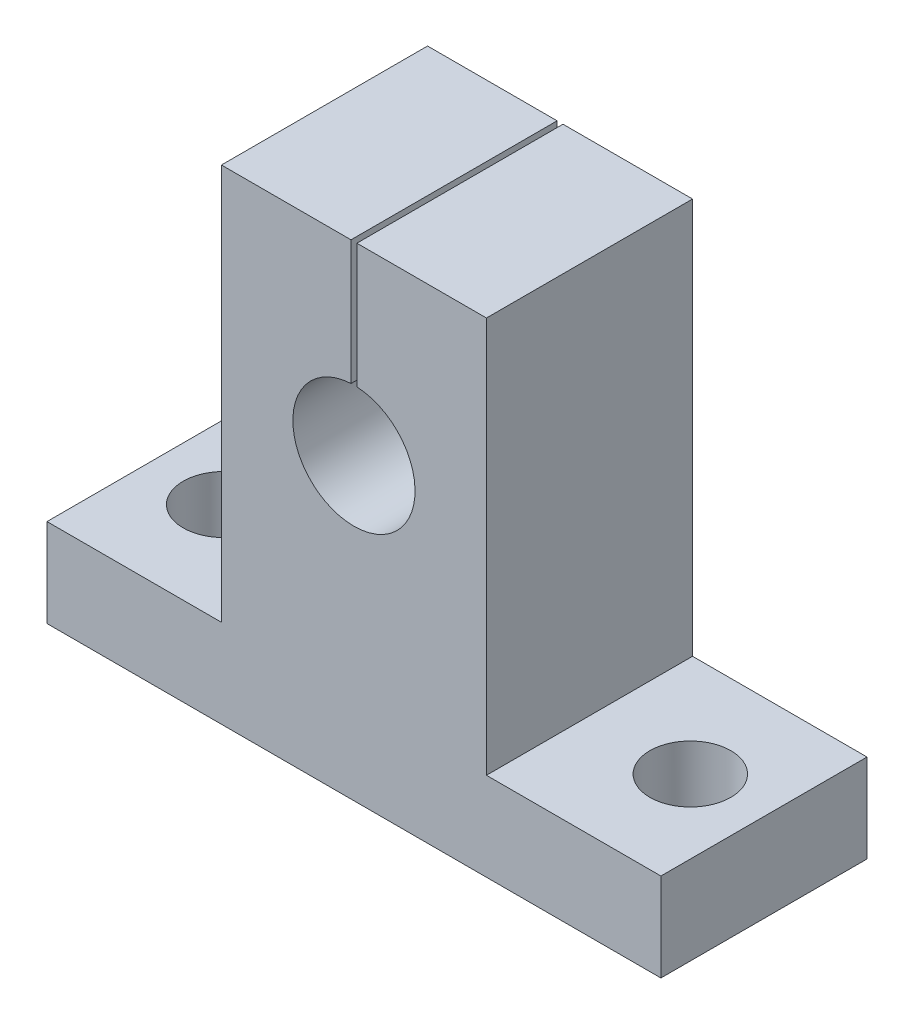
SolidWorks part; units mm, degrees
ref_plane "Front Plane" through (0, 0, 0) normal (0, 0, 1) x (1, 0, 0)
ref_plane "Top Plane" through (0, 0, 0) normal (0, 1, 0) x (1, 0, 0)
ref_plane "Right Plane" through (0, 0, 0) normal (1, 0, 0) x (0, 0, -1)
sketch "Sketch1" plane through (0, 0, 0) normal (0, 0, 1) x (1, 0, 0)
  line L0 (-20.85, 0) -> (20.85, 0)
  line L1 (-20.85, 0) -> (-20.85, 6)
  line L2 (-20.85, 6) -> (-9, 6)
  line L3 (-9, 6) -> (-9, 32.9)
  line L4 (-9, 32.9) -> (-0.2, 32.9)
  line L5 (-0.2, 32.9) -> (-0.2, 20.3)
  line L6 (-0.2, 20.3) -> (0.2, 20.3)
  line L7 (0.2, 20.3) -> (0.2, 32.9)
  line L8 (0.2, 32.9) -> (9, 32.9)
  line L9 (9, 32.9) -> (9, 6)
  line L10 (9, 6) -> (20.85, 6)
  line L11 (20.85, 6) -> (20.85, 0)
  circle A0 centre (0, 20.3) radius 4.15
  point P3 (0, 0)
  point P11 (0, 0)
  point P15 (0, 19.4544)
  point P18 (0, 19.1706)
  point P19 (0.2258, 23.9161)
  point P20 (-0.2, 19.1706)
  point P21 (0.2, 19.6634)
  point P22 (0, 20.3)
  point P23 (0.2, 21.6068)
  dimension "D5" = 8.3
  dimension "D1" = 41.7
  dimension "D2" = 6
  dimension "D3" = 32.9
  dimension "D4" = 18
  dimension "D6" = 0.4
  dimension "D7" = 20.3
extrude "Boss-Extrude1" add sketch "Sketch1" along normal blind 14 contours A0 L5 L4 L3 L2 L1 L0 L11 L10 L9 L8 L7
sketch "Sketch2" plane through (0, 0, 0) normal (0, -1, 0) x (1, 0, 0)
  line L0 (-15.85, 7) -> (15.85, 7) construction
  line L1 (-20.85, 14) -> (-20.85, 0) construction
  circle A0 centre (-15.85, 7) radius 2.75
  circle A1 centre (15.85, 7) radius 2.75
  point P4 (0, 7)
  point P8 (-20.85, 7)
  dimension "D2" = 5.5
  dimension "D1" = 31.7
extrude "Cut-Extrude1" cut sketch "Sketch2" against normal through all
